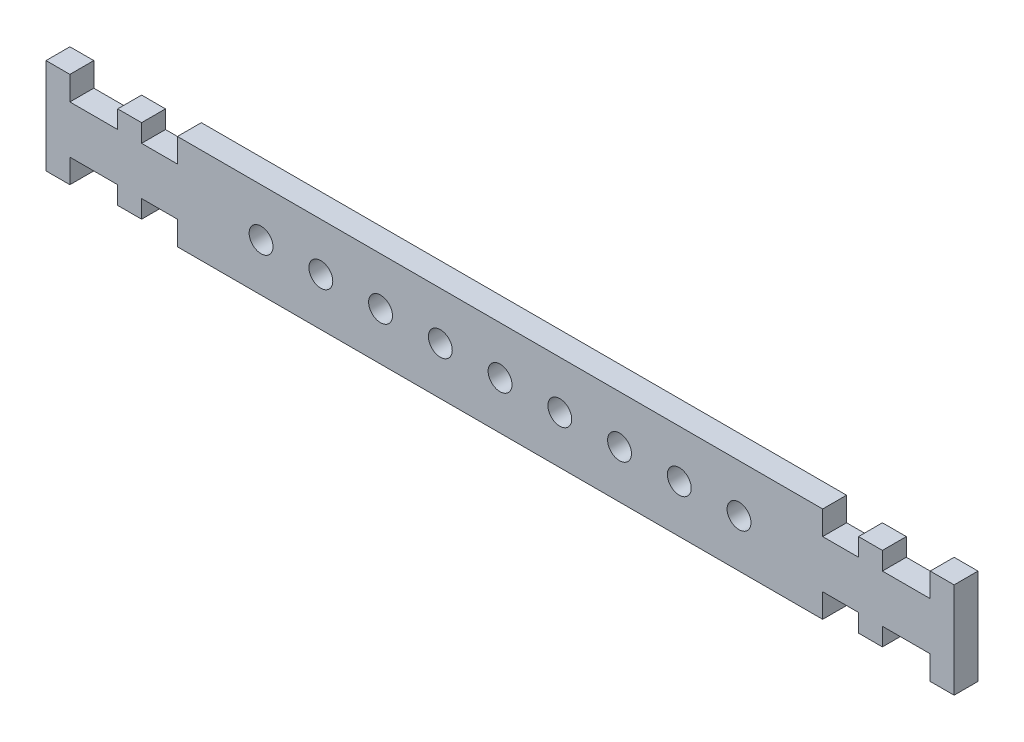
SolidWorks part; units mm, degrees
ref_plane "前视基准面" through (0, 0, 0) normal (0, 0, 1) x (1, 0, 0)
ref_plane "上视基准面" through (0, 0, 0) normal (0, 1, 0) x (1, 0, 0)
ref_plane "右视基准面" through (0, 0, 0) normal (1, 0, 0) x (0, 0, -1)
other "Configuration Table"
sketch "草图1" plane through (0, 0, 0) normal (0, 0, 1) x (1, 0, 0)
  line L0 (0, 0) -> (27.0318, 0) construction
  line L1 (0, -1.1987) -> (0, -17.6851) construction
  line L2 (-27, 4) -> (27, 4)
  line L3 (27, 4) -> (27, 2)
  line L4 (27, 2) -> (30, 2)
  line L5 (30, 2) -> (30, 3.5)
  line L6 (30, 3.5) -> (32, 3.5)
  line L7 (32, 3.5) -> (32, 2)
  line L8 (32, 2) -> (36, 2)
  line L9 (36, 2) -> (36, 4)
  line L10 (36, 4) -> (38, 4)
  line L11 (38, 4) -> (38, -4)
  line L12 (38, -4) -> (36, -4)
  line L13 (36, -4) -> (36, -2)
  line L14 (36, -2) -> (32, -2)
  line L15 (32, -2) -> (32, -3.5)
  line L16 (32, -3.5) -> (30, -3.5)
  line L17 (30, -3.5) -> (30, -2)
  line L18 (30, -2) -> (27, -2)
  line L19 (27, -2) -> (27, -4)
  line L20 (27, -4) -> (-27, -4)
  line L21 (-27, -2) -> (-27, -4)
  line L22 (-30, -2) -> (-27, -2)
  line L23 (-30, -3.5) -> (-30, -2)
  line L24 (-32, -3.5) -> (-30, -3.5)
  line L25 (-32, -2) -> (-32, -3.5)
  line L26 (-36, -2) -> (-32, -2)
  line L27 (-36, -4) -> (-36, -2)
  line L28 (-38, -4) -> (-36, -4)
  line L29 (-38, 4) -> (-38, -4)
  line L30 (-36, 4) -> (-38, 4)
  line L31 (-36, 2) -> (-36, 4)
  line L32 (-32, 2) -> (-36, 2)
  line L33 (-32, 3.5) -> (-32, 2)
  line L34 (-30, 3.5) -> (-32, 3.5)
  line L35 (-30, 2) -> (-30, 3.5)
  line L36 (-27, 2) -> (-30, 2)
  line L37 (-27, 4) -> (-27, 2)
  circle A0 centre (0, 0) radius 1
  circle A1 centre (5, 0) radius 1
  circle A2 centre (10, 0) radius 1
  circle A3 centre (15, 0) radius 1
  circle A4 centre (20, 0) radius 1
  circle A5 centre (-5, 0) radius 1
  circle A6 centre (-10, 0) radius 1
  circle A7 centre (-15, 0) radius 1
  circle A8 centre (-20, 0) radius 1
  point P6 (0, -4)
  point P43 (0, 4)
  dimension "D14" = 2
  dimension "D1" = 27
  dimension "D2" = 2
  dimension "D3" = 3
  dimension "D4" = 1.5
  dimension "D5" = 4
  dimension "D6" = 2
  dimension "D7" = 2
  dimension "D8" = 2
  dimension "D9" = 8
  dimension "D10" = 4
  dimension "D11" = 4
  dimension "D12" = 64
  dimension "D13" = 54
  dimension "D15" = 5
  dimension "D16" = 5
extrude "凸台-拉伸1" add sketch "草图1" along normal blind 2
